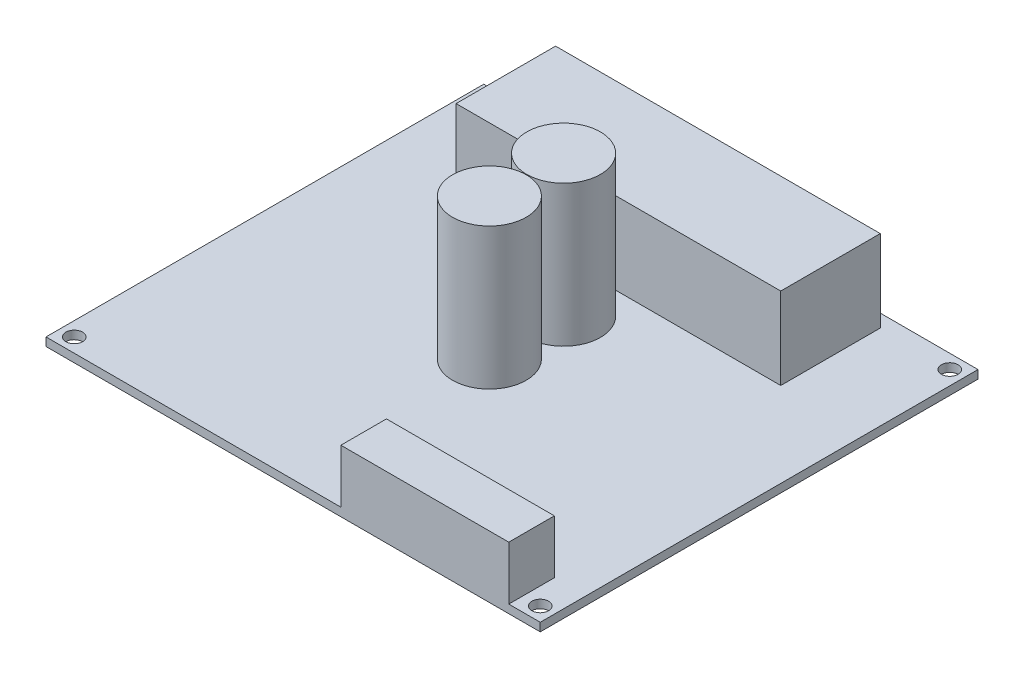
SolidWorks part; units mm, degrees
ref_plane "Front Plane" through (0, 0, 0) normal (0, 0, 1) x (1, 0, 0)
ref_plane "Top Plane" through (0, 0, 0) normal (0, 1, 0) x (1, 0, 0)
ref_plane "Right Plane" through (0, 0, 0) normal (1, 0, 0) x (0, 0, -1)
sketch "Sketch1" plane through (0, 0, 0) normal (0, 1, 0) x (1, 0, 0)
  line L1 (44.45, -39.37) -> (-44.45, -39.37)
  line L2 (44.45, -39.37) -> (44.45, 39.37)
  line L3 (44.45, 39.37) -> (-44.45, 39.37)
  line L4 (-44.45, -39.37) -> (-44.45, 39.37)
  line L5 (44.45, -39.37) -> (-44.45, 39.37) construction
  line L6 (44.45, 39.37) -> (-44.45, -39.37) construction
  line L7 (41.91, -36.83) -> (-41.91, -36.83) construction
  line L8 (41.91, -36.83) -> (41.91, 36.83) construction
  line L9 (41.91, 36.83) -> (-41.91, 36.83) construction
  line L10 (-41.91, -36.83) -> (-41.91, 36.83) construction
  line L11 (41.91, -36.83) -> (-41.91, 36.83) construction
  line L12 (41.91, 36.83) -> (-41.91, -36.83) construction
  circle A0 centre (-41.91, 36.83) radius 1.5
  circle A1 centre (41.91, 36.83) radius 1.5
  circle A2 centre (41.91, -36.83) radius 1.5
  circle A3 centre (-41.91, -36.83) radius 1.5
  point P0 (0, 0)
  point P7 (0, 0)
  dimension "D5" = 3
  dimension "D1" = 88.9
  dimension "D2" = 78.74
  dimension "D3" = 83.82
  dimension "D4" = 73.66
extrude "Boss-Extrude1" add sketch "Sketch1" along normal blind 1.5
sketch "Sketch2" plane through (0, 1.5, 0) normal (0, 1, 0) x (1, 0, 0)
  line L0 (44.45, 39.37) -> (-44.45, 39.37) construction
  line L1 (-29.2, 19.14) -> (29.2, 19.14)
  line L2 (-29.2, 19.14) -> (-29.2, 37.04)
  line L3 (-29.2, 37.04) -> (29.2, 37.04)
  line L4 (29.2, 19.14) -> (29.2, 37.04)
  line L5 (-29.2, 19.14) -> (29.2, 37.04) construction
  line L6 (-29.2, 37.04) -> (29.2, 19.14) construction
  point P0 (0, 28.09)
  dimension "D1" = 58.4
  dimension "D2" = 17.9
  dimension "D3" = 2.33
extrude "Boss-Extrude2" add sketch "Sketch2" along normal blind 14.72
sketch "Sketch3" plane through (0, 1.5, 0) normal (0, 1, 0) x (1, 0, 0)
  line L0 (44.45, -39.37) -> (44.45, 39.37) construction
  line L1 (8.59, -39.37) -> (38.79, -39.37)
  line L2 (8.59, -39.37) -> (8.59, -31.17)
  line L3 (8.59, -31.17) -> (38.79, -31.17)
  line L4 (38.79, -39.37) -> (38.79, -31.17)
  line L5 (8.59, -39.37) -> (38.79, -31.17) construction
  line L6 (8.59, -31.17) -> (38.79, -39.37) construction
  line L7 (-44.45, -39.37) -> (44.45, -39.37) construction
  point P0 (23.69, -35.27)
  dimension "D1" = 30.2
  dimension "D2" = 8.2
  dimension "D3" = 5.66
extrude "Boss-Extrude3" add sketch "Sketch3" along normal blind 9.65
sketch "Sketch4" plane through (0, 1.5, 0) normal (0, 1, 0) x (1, 0, 0)
  line L0 (-44.45, 39.37) -> (-44.45, -39.37) construction
  line L1 (-44.45, -39.37) -> (8.59, -39.37) construction
  circle A0 centre (-1.125, 10.405) radius 6.625
  circle A1 centre (-1.125, -2.945) radius 6.625
  point P8 (-1.125, 11.7595)
  dimension "D1" = 13.25
  dimension "D2" = 43.325
  dimension "D3" = 36.425
  dimension "D4" = 13.35
extrude "Boss-Extrude6" add sketch "Sketch4" along normal blind 25.4
equation "\"D2@Sketch4\"=36.7+\"D1@Sketch4\"/2"
equation "\"D3@Sketch4\"=29.8+\"D1@Sketch4\"/2"
equation "\"D4@Sketch4\"=\"D1@Sketch4\"+.1"
